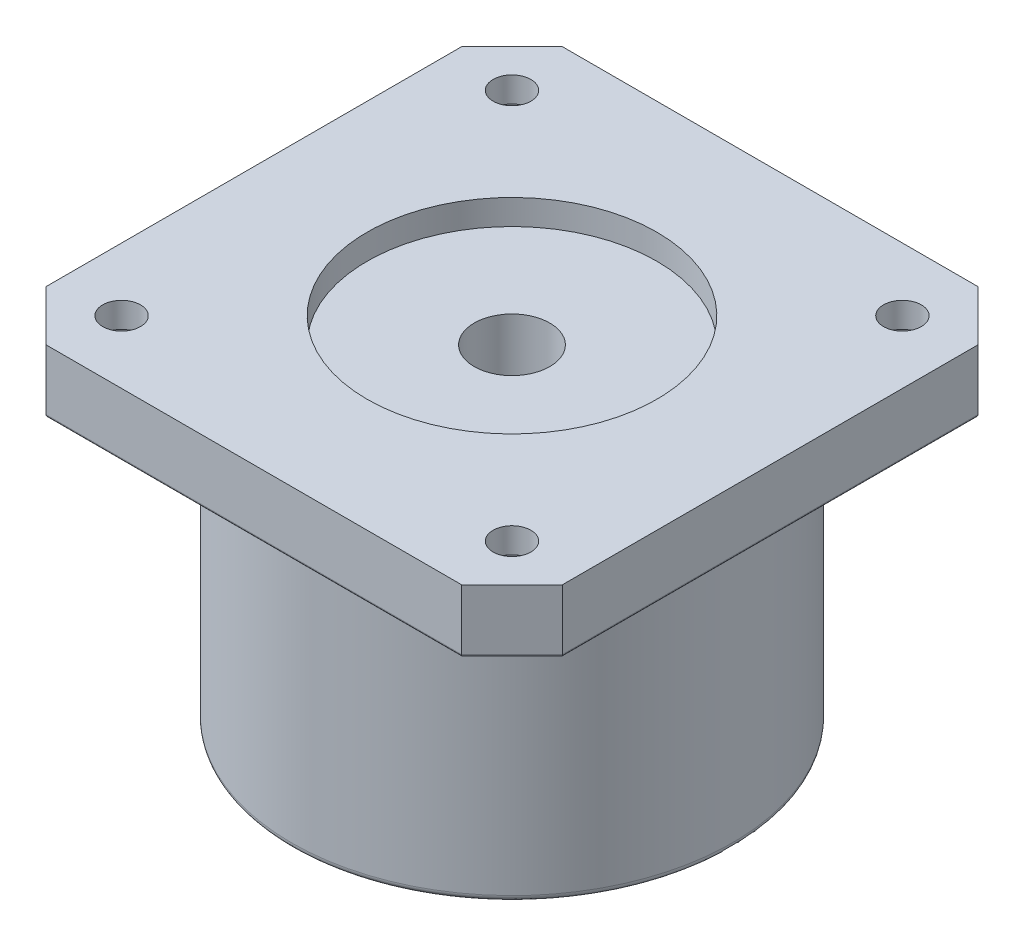
SolidWorks part; units mm, degrees
ref_plane "Front Plane" through (0, 0, 0) normal (0, 0, 1) x (1, 0, 0)
ref_plane "Top Plane" through (0, 0, 0) normal (0, 1, 0) x (1, 0, 0)
ref_plane "Right Plane" through (0, 0, 0) normal (1, 0, 0) x (0, 0, -1)
sketch "Sketch1" plane through (0, 0, 0) normal (0, 1, 0) x (1, 0, 0)
  line L1 (0, 0) -> (41, 0)
  line L2 (0, 0) -> (0, 41)
  line L3 (0, 41) -> (41, 41)
  line L4 (41, 0) -> (41, 41)
  dimension "D1" = 41
  dimension "D2" = 41
extrude "Boss-Extrude1" add sketch "Sketch1" along normal blind 5
sketch "Sketch2" plane through (0, 5, 0) normal (0, 1, 0) x (1, 0, 0)
  line L0 (0, 0) -> (0, 4)
  line L1 (0, 41) -> (0, 0) construction
  line L2 (0, 4) -> (4, 0)
  line L3 (0, 0) -> (41, 0) construction
  line L4 (4, 0) -> (0, 0)
  line L5 (37, 0) -> (41, 4)
  line L6 (41, 0) -> (41, 41) construction
  line L7 (41, 4) -> (41, 0)
  line L8 (41, 0) -> (37, 0)
  line L9 (37, 41) -> (41, 41)
  line L10 (41, 41) -> (0, 41) construction
  line L11 (41, 41) -> (41, 37)
  line L12 (41, 37) -> (37, 41)
  line L13 (0, 42.1095) -> (0, 41)
  line L14 (0, 41) -> (0, 37)
  line L15 (0, 37) -> (4, 41)
  line L16 (4, 41) -> (0, 41)
  line M4 (0, 41) -> (0, 0)
  line M5 (0, 0) -> (41, 0)
  line M6 (41, 0) -> (41, 41)
  line M7 (41, 41) -> (0, 41)
  dimension "D1" = 4
  dimension "D2" = 4
  dimension "D3" = 4
  dimension "D4" = 4
  dimension "D5" = 4
  dimension "D6" = 4
  dimension "D7" = 4
  dimension "D8" = 4
extrude "Cut-Extrude2" cut sketch "Sketch2" against normal blind 5 contours L2 M4 M5 | L15 M4 M7 | L12 M6 M7 | L5 M5 M6
sketch "Sketch4" plane through (0, 5, 0) normal (0, 1, 0) x (1, 0, 0)
  line L0 (0, 37) -> (0, 4) construction
  line L1 (4, 0) -> (37, 0) construction
  circle A0 centre (20.5, 20.5) radius 11.5
  dimension "D1" = 23
  dimension "D2" = 20.5
  dimension "D3" = 20.5
extrude "Cut-Extrude3" cut sketch "Sketch4" against normal blind 2
sketch "Sketch5" plane through (0, 5, 0) normal (0, 1, 0) x (1, 0, 0)
  circle A4 centre (20.5, 20.5) radius 3
  point P2 (20.5, 20.5)
  dimension "D6" = 6
sketch "Sketch6" plane through (0, 0, 0) normal (0, -1, 0) x (1, 0, 0)
  circle A0 centre (20.5, -20.5) radius 17.5
  dimension "D1" = 35
extrude "Boss-Extrude2" add sketch "Sketch6" along normal blind 23
fillet "Fillet1" radius 0.2 8 edges at (2, 0, -39) (0, 0, -20.5) (2, 0, -2) (20.5, 0, -41) (39, 0, -39) (41, 0, -20.5) (39, 0, -2) (20.5, 0, 0)
fillet "Fillet2" radius 0.5 1 edges at (20.5, -23, -38)
sketch "Sketch13" plane through (0, -23, 0) normal (0, -1, 0) x (-1, 0, 0)
  circle A0 centre (-20.5, 20.5) radius 11
  dimension "D1" = 22
extrude "Boss-Extrude3" add sketch "Sketch13" along normal blind 2 contours A0
extrude "Cut-Extrude9" cut sketch "Sketch5" against normal through all contours A4
sketch "Sketch14" plane through (0, -23, 0) normal (0, -1, 0) x (-1, 0, 0)
  line L0 (-20.5, 20.5) -> (-20.5, -1.0982) construction
  circle A0 centre (-20.5, 6.5) radius 2.5
  circle A2 centre (-34.5, 20.5) radius 2.5
  circle A3 centre (-20.5, 34.5) radius 2.5
  circle A4 centre (-6.5, 20.5) radius 2.5
  point P14 (-20.5, 20.5)
  dimension "D2" = 5
  dimension "D1" = 14
  dimension "D3" = 4
sketch "Sketch15" plane through (0, -23, 0) normal (0, -1, 0) x (-1, 0, 0)
  line L0 (-36.9172, 0.2) -> (-4.0828, 0.2) construction
  line L1 (-0.2, 4.0828) -> (-0.2, 36.9172) construction
  circle A0 centre (-6.3579, 20.5) radius 1.5
  circle A1 centre (-30.5, 10.5) radius 1.5
  circle A2 centre (-20.5, 6.3579) radius 1.5
  circle A3 centre (-30.5, 30.5) radius 1.5
  circle A4 centre (-34.6421, 20.5) radius 1.5
  circle A5 centre (-10.5, 30.5) radius 1.5
  circle A6 centre (-20.5, 34.6421) radius 1.5
  circle A7 centre (-10.5, 10.5) radius 1.5
  point P0 (-20.5, 0.2)
  point P3 (-0.2, 20.5)
  point P21 (-20.5, 20.5)
  point P25 (-20.5, 20.5)
  dimension "D1" = 3
  dimension "D2" = 20.3
  dimension "D9" = 14.1421
  dimension "D3" = 20.3
  dimension "D4" = 10
  dimension "D5" = 10
  dimension "D6" = 14.1421
  dimension "D7" = 10
  dimension "D8" = 2
extrude "Cut-Extrude10" cut sketch "Sketch14" against normal blind 5
extrude "Cut-Extrude11" cut sketch "Sketch15" against normal blind 5
sketch "Sketch16" plane through (0, 0, 0) normal (0, -1, 0) x (-1, 0, 0)
  circle A0 centre (-5, 5) radius 2.5
  circle A1 centre (-36, 5) radius 2.5
  circle A2 centre (-5, 36) radius 2.5
  circle A3 centre (-36, 36) radius 2.5
  dimension "D1" = 5
  dimension "D2" = 5
  dimension "D3" = 15.5
  dimension "D4" = 15.5
  dimension "D5" = 15.5
  dimension "D6" = 15.5
  dimension "D7" = 2
extrude "Cut-Extrude12" cut sketch "Sketch16" against normal blind 3
sketch "Sketch17" plane through (0, 3, 0) normal (0, -1, 0) x (-1, 0, 0)
  circle A0 centre (-5, 5) radius 1.5
  circle A1 centre (-36, 5) radius 1.5
  circle A2 centre (-5, 36) radius 1.5
  circle A3 centre (-36, 36) radius 1.5
  point P7 (-20.5, 20.5)
  dimension "D1" = 3
  dimension "D4" = 15.5
  dimension "D2" = 15.5
  dimension "D3" = 15.5
  dimension "D5" = 2
extrude "Cut-Extrude13" cut sketch "Sketch17" against normal through all
sketch "Sketch18" plane through (0, -18, 0) normal (0, -1, 0) x (1, 0, 0)
  circle A0 centre (6.5, -20.5) radius 1.5
  circle A1 centre (34.5, -20.5) radius 1.5
  circle A2 centre (20.5, -6.5) radius 1.5
  circle A3 centre (20.5, -34.5) radius 1.5
  dimension "D1" = 3
extrude "Cut-Extrude14" cut sketch "Sketch18" against normal blind 5
